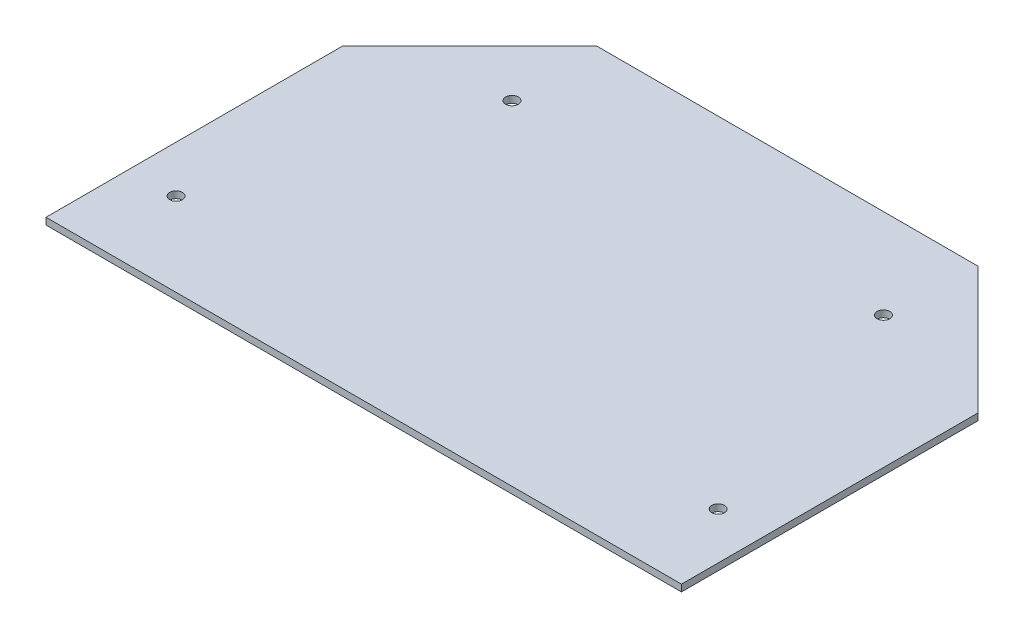
SolidWorks part; units mm, degrees
ref_plane "Front Plane" through (0, 0, 0) normal (0, 0, 1) x (1, 0, 0)
ref_plane "Top Plane" through (0, 0, 0) normal (0, 1, 0) x (1, 0, 0)
ref_plane "Right Plane" through (0, 0, 0) normal (1, 0, 0) x (0, 0, -1)
sketch "Sketch1" plane through (0, 0, 0) normal (0, 1, 0) x (1, 0, 0)
  line L1 (-75, -35) -> (-75, 35)
  line L2 (-75, 35) -> (-45, 65)
  line L3 (-45, 65) -> (0, 65)
  line L4 (0, -35) -> (0, 65)
  line L5 (0, -35) -> (-75, -35)
  line L6 (-59.397, 28.2843) -> (-43.8406, 43.8406) construction
  line L7 (-51.9976, -33.7676) -> (-63.9796, -15.3169) construction
  line L9 (0, 0) -> (-85, 0) construction
  line L10 (-43.8406, 43.8406) -> (0, 0) construction
  line L11 (-51.9976, -33.7676) -> (0, 0) construction
  circle A0 centre (0, 0) radius 85 construction
  circle A1 centre (-43.8406, 43.8406) radius 1.5
  circle A4 centre (-63.9796, -15.3169) radius 1.5
  dimension "D7" = 3
  dimension "D17" = 170
  dimension "D2" = 100
  dimension "D3" = 70
  dimension "D5" = 35
  dimension "D6" = 75
  dimension "D8" = 62
  dimension "D9" = 22
  dimension "D10" = 22
  dimension "D14" = 45
  dimension "D15" = 33
extrude "Boss-Extrude1" add sketch "Sketch1" along normal blind 1.6
mirror "Mirror1" about plane through (0, 1.6, 35) normal (-1, 0, 0) of "Boss-Extrude1"
